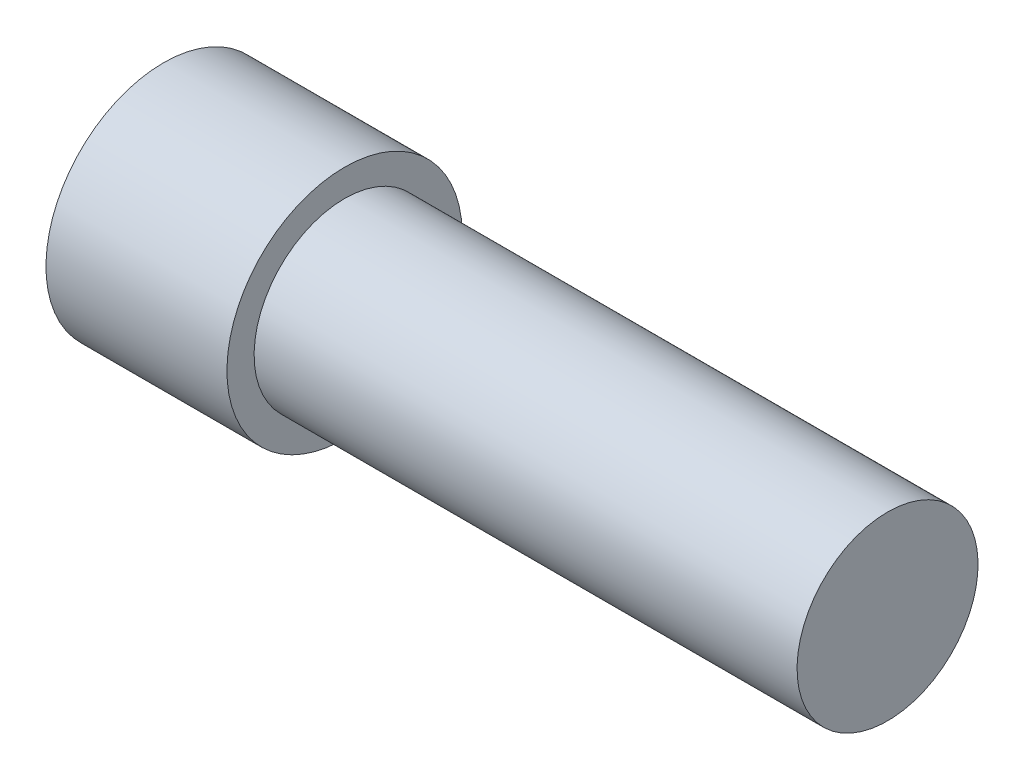
SolidWorks part; units mm, degrees
ref_plane "Front Plane" through (0, 0, 0) normal (0, 0, 1) x (1, 0, 0)
ref_plane "Top Plane" through (0, 0, 0) normal (0, 1, 0) x (1, 0, 0)
ref_plane "Right Plane" through (0, 0, 0) normal (1, 0, 0) x (0, 0, -1)
sketch "Sketch1" plane through (0, 0, 0) normal (0, 0, 1) x (1, 0, 0)
  line L0 (-20, 0) -> (-20, 6.5)
  line L1 (-20, 6.5) -> (-10, 6.5)
  line L2 (-10, 6.5) -> (-10, 5)
  line L3 (-10, 5) -> (20, 5)
  line L4 (20, 5) -> (20, 0)
  line L5 (20, 0) -> (-20, 0)
  dimension "D1" = 10
  dimension "D2" = 30
  dimension "D3" = 6.5
  dimension "D4" = 5
  dimension "D5" = 20
  dimension "D6" = 6.5
revolve "Revolve1" add sketch "Sketch1" angle 360 about L5
sketch "Sketch2" plane through (-20, 0, 0) normal (-1, 0, 0) x (0, 0, 1)
  line L1 (5.1962, 0) -> (2.5981, 4.5)
  line L2 (2.5981, 4.5) -> (-2.5981, 4.5)
  line L3 (-2.5981, 4.5) -> (-5.1962, 0)
  line L4 (-5.1962, 0) -> (-2.5981, -4.5)
  line L5 (-2.5981, -4.5) -> (2.5981, -4.5)
  line L6 (2.5981, -4.5) -> (5.1962, 0)
  circle A0 centre (0, 0) radius 4.5 construction
  point P1 (0, 0)
  dimension "D1" = 9
extrude "Cut-Extrude1" cut sketch "Sketch2" against normal blind 9
